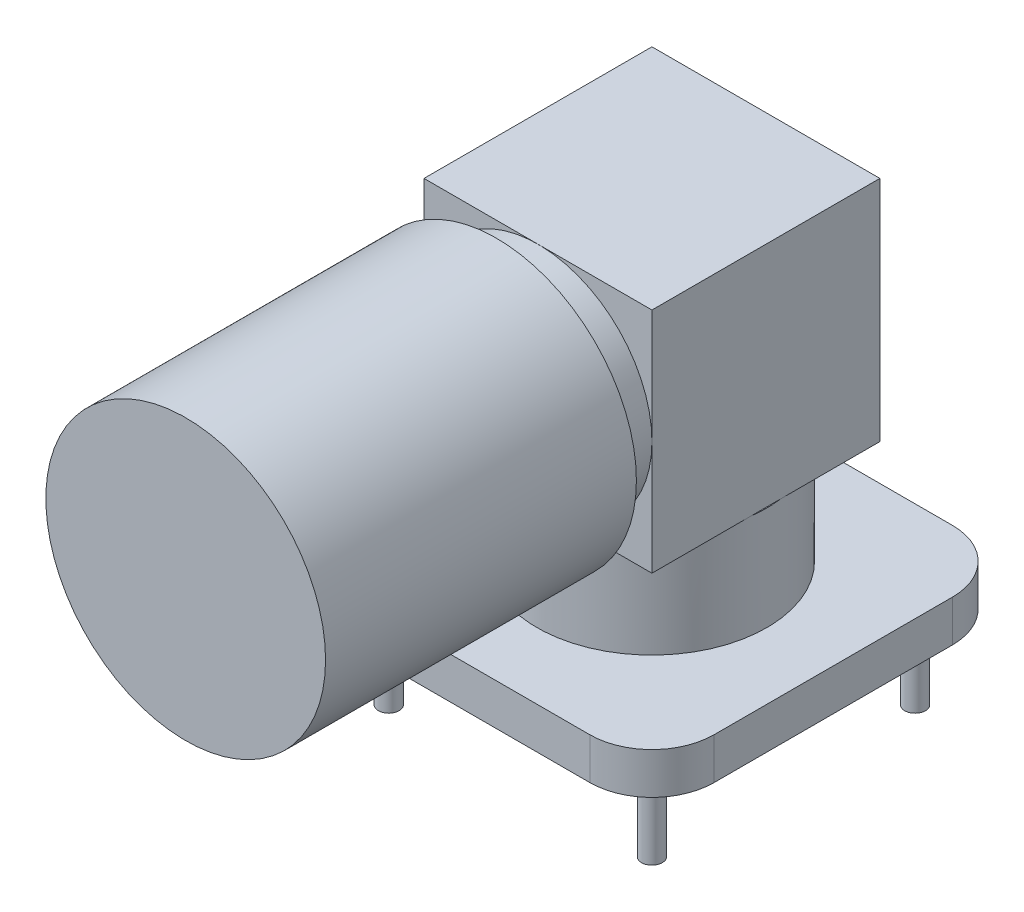
SolidWorks part; units mm, degrees
ref_plane "Ebene vorne" through (0, 0, 0) normal (0, 0, 1) x (1, 0, 0)
ref_plane "Ebene oben" through (0, 0, 0) normal (0, 1, 0) x (1, 0, 0)
ref_plane "Ebene rechts" through (0, 0, 0) normal (1, 0, 0) x (0, 0, -1)
sketch "Skizze1" plane through (0, 0, 0) normal (0, 1, 0) x (1, 0, 0)
  line L1 (-5.75, -8.75) -> (5.75, -8.75)
  line L2 (-8.75, -5.75) -> (-8.75, 5.75)
  line L3 (-5.75, 8.75) -> (5.75, 8.75)
  line L4 (8.75, -5.75) -> (8.75, 5.75)
  line L5 (-8.75, -8.75) -> (8.75, 8.75) construction
  line L6 (-8.75, 8.75) -> (8.75, -8.75) construction
  arc A0 (-5.75, -8.75) -> (-8.75, -5.75) centre (-5.75, -5.75) cw
  arc A1 (5.75, -8.75) -> (8.75, -5.75) centre (5.75, -5.75) ccw
  arc A2 (5.75, 8.75) -> (8.75, 5.75) centre (5.75, 5.75) cw
  arc A3 (-8.75, 5.75) -> (-5.75, 8.75) centre (-5.75, 5.75) cw
  point P0 (0, 0)
  dimension "D3" = 3
  dimension "D1" = 17.5
  dimension "D2" = 17.5
extrude "Aufsatz-Linear austragen1" add sketch "Skizze1" along normal blind 2
sketch "Skizze2" plane through (0, 0, 0) normal (0, -1, 0) x (1, 0, 0)
  line L1 (-6.35, 6.35) -> (6.35, 6.35) construction
  line L2 (-6.35, 6.35) -> (-6.35, -6.35) construction
  line L3 (-6.35, -6.35) -> (6.35, -6.35) construction
  line L4 (6.35, 6.35) -> (6.35, -6.35) construction
  line L5 (-6.35, 6.35) -> (6.35, -6.35) construction
  line L6 (-6.35, -6.35) -> (6.35, 6.35) construction
  circle A0 centre (6.35, -6.35) radius 0.5
  circle A1 centre (-6.35, 6.35) radius 0.5
  circle A2 centre (6.35, 6.35) radius 0.5
  circle A3 centre (-6.35, -6.35) radius 0.5
  circle A4 centre (0, 0) radius 0.5
  point P0 (0, 0)
  dimension "D2" = 1
  dimension "D1" = 12.7
extrude "Aufsatz-Linear austragen2" add sketch "Skizze2" along normal blind 4
sketch "Skizze3" plane through (0, 2, 0) normal (0, 1, 0) x (1, 0, 0)
  circle A0 centre (0, 0) radius 5.55
  dimension "D1" = 11.1
extrude "Aufsatz-Linear austragen3" add sketch "Skizze3" along normal blind 5
sketch "Skizze4" plane through (0, 7, 0) normal (0, 1, 0) x (1, 0, 0)
  line L1 (-5.5, 5.5) -> (5.5, 5.5)
  line L2 (-5.5, 5.5) -> (-5.5, -5.5)
  line L3 (-5.5, -5.5) -> (5.5, -5.5)
  line L4 (5.5, 5.5) -> (5.5, -5.5)
  line L5 (-5.5, 5.5) -> (5.5, -5.5) construction
  line L6 (-5.5, -5.5) -> (5.5, 5.5) construction
  point P0 (0, 0)
  dimension "D1" = 11
extrude "Aufsatz-Linear austragen4" add sketch "Skizze4" along normal blind 11
sketch "Skizze5" plane through (0, 0, 5.5) normal (0, 0, 1) x (1, 0, 0)
  line L0 (-5.5, 18) -> (5.5, 7) construction
  line L3 (5.5, 18) -> (-5.5, 7) construction
  circle A0 centre (0, 12.5) radius 5.5
  point P9 (0, 12.5)
  dimension "D1" = 11
extrude "Aufsatz-Linear austragen6" add sketch "Skizze5" along normal blind 10 separate body
sketch "Skizze6" plane through (0, 0, 5.5) normal (0, 0, 1) x (1, 0, 0)
  circle A0 centre (0, 12.5) radius 6.75
  dimension "D1" = 13.5
extrude "Aufsatz-Linear austragen7" add sketch "Skizze6" along normal blind 15 from offset 2 separate body
